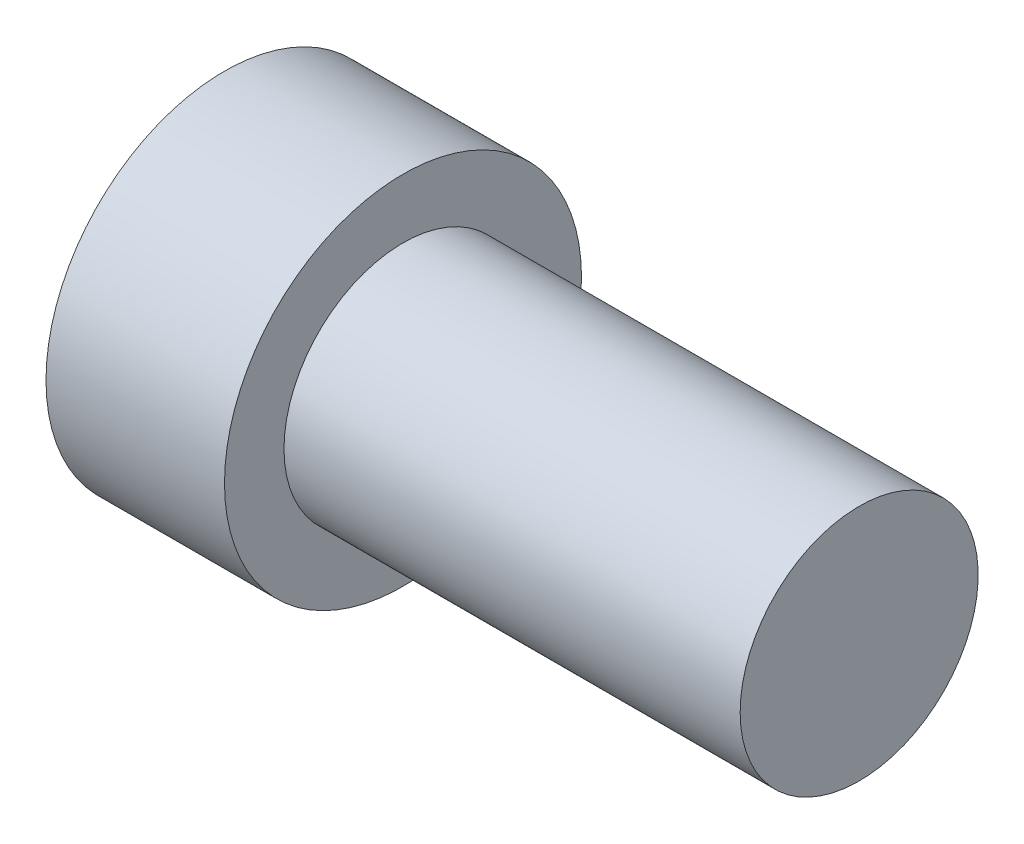
SolidWorks part; units mm, degrees
ref_plane "Ebene vorne" through (0, 0, 0) normal (0, 0, 1) x (1, 0, 0)
ref_plane "Ebene oben" through (0, 0, 0) normal (0, 1, 0) x (1, 0, 0)
ref_plane "Ebene rechts" through (0, 0, 0) normal (1, 0, 0) x (0, 0, -1)
sketch "Skizze3" plane through (0, 0, 0) normal (0, 1, 0) x (1, 0, 0)
  line L0 (0, 0) -> (32, 0)
  line L1 (32, 0) -> (32, 6)
  line L2 (32, 6) -> (9, 6)
  line L3 (9, 6) -> (9, 9)
  line L4 (9, 9) -> (0, 9)
  line L5 (0, 9) -> (0, 0)
  dimension "D1" = 9
  dimension "D2" = 32
  dimension "D3" = 9
  dimension "D4" = 6
revolve "Rotation1" add sketch "Skizze3" angle 360 about L0
sketch "Skizze4" plane through (0, 0, 0) normal (-1, 0, 0) x (0, 0, 1)
  circle A0 centre (0, 0) radius 2.5
  dimension "D1" = 5
extrude "Schnitt-Linear austragen1" cut sketch "Skizze4" against normal blind 20.5
